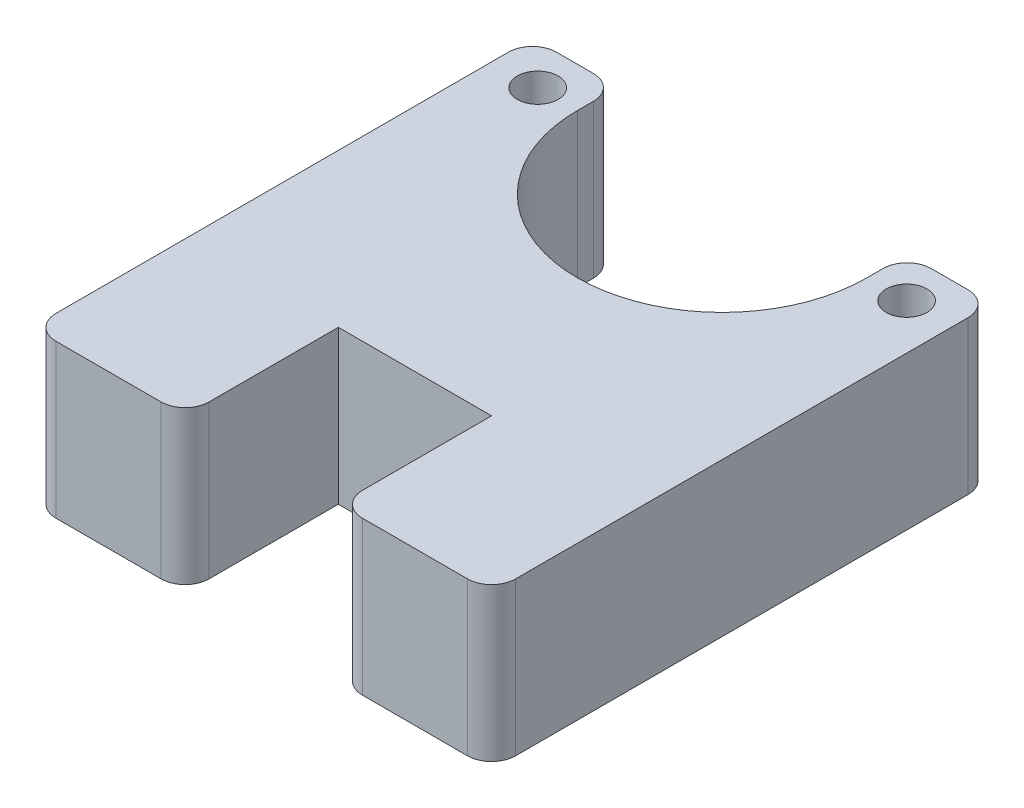
SolidWorks part; units mm, degrees
ref_plane "Front Plane" through (0, 0, 0) normal (0, 0, 1) x (1, 0, 0)
ref_plane "Top Plane" through (0, 0, 0) normal (0, 1, 0) x (1, 0, 0)
ref_plane "Right Plane" through (0, 0, 0) normal (1, 0, 0) x (0, 0, -1)
sketch "Sketch1" plane through (0, 0, 0) normal (0, 1, 0) x (1, 0, 0)
  line L0 (0, 0) -> (0, 6.0001)
  line L1 (0, 0) -> (19.05, 0)
  line L2 (0, 6.0001) -> (19.05, 6.0001)
  line L3 (19.05, 0) -> (19.05, 6.0001)
  line L4 (0, 6.0001) -> (0, 14.3937)
  line L5 (0, 6.0001) -> (3.525, 6.0001)
  line L6 (0, 14.3937) -> (3.525, 14.3937)
  line L7 (3.525, 6.0001) -> (3.525, 14.3937)
  line L8 (19.05, 6.0001) -> (19.05, 14.3937)
  line L9 (19.05, 6.0001) -> (15.525, 6.0001)
  line L10 (19.05, 14.3937) -> (15.525, 14.3937)
  line L11 (15.525, 6.0001) -> (15.525, 14.3937)
  line L12 (0, 0) -> (6.35, 0)
  line L13 (0, 0) -> (0, -6.35)
  line L14 (6.35, 0) -> (6.35, -6.35)
  line L15 (0, -6.35) -> (6.35, -6.35)
  line L16 (19.05, 0) -> (12.7, 0)
  line L17 (19.05, 0) -> (19.05, -6.35)
  line L18 (12.7, 0) -> (12.7, -6.35)
  line L19 (19.05, -6.35) -> (12.7, -6.35)
  arc A0 (3.525, 12.7287) -> (15.525, 12.7287) centre (9.525, 12.7287) ccw
  circle A1 centre (17.1675, 12.7287) radius 0.845
  circle A2 centre (1.8825, 12.7287) radius 0.845
  point P8 (9.525, 6.0001)
  dimension "D6" = 1.69
  dimension "D1" = 6.0001
  dimension "D2" = 6.35
  dimension "D3" = 6.7286
  dimension "D4" = 6
  dimension "D5" = 1.665
  dimension "D7" = 1.6425
  dimension "D9" = 6.35
  dimension "D10" = 6.35
  dimension "D11" = 6.35
  dimension "D12" = 6.35
  dimension "D13" = 1.6425
extrude "Boss-Extrude1" add sketch "Sketch1" along normal blind 6.35 contours L2 L7 L6 L4 A2 | A0 L7 L2 L11 | L11 L2 L8 L10 A1 | L1 L3 L2 L0 | L13 L15 L14 L1 | L19 L17 L1 L18
fillet "Fillet3" radius 1 8 edges at (19.05, 3.175, 6.35) (12.7, 3.175, 6.35) (6.35, 3.175, 6.35) (0, 3.175, 6.35) (19.05, 3.175, -14.3937) (15.525, 3.175, -14.3937) (3.525, 3.175, -14.3937) (0, 3.175, -14.3937)
equation "\"vigorwidth\"= 0.472441in"
equation "\"vigorflangewidth\"= 0.731102in"
equation "\"vigorflangelength\"= 0.131102in"
equation "\"vigorscrewsize\"= 0.066535in"
equation "\"vigorholeoffsetwid\"= 0.0646653in"
equation "\"vigorholeoffsetlen\"= 0.065551in"
equation "\"vigorflangedepth\"= 0.0901575in"
equation "\"vigordiscdepth\"= 0.0492126in"
equation "\"vigormotordepth\"= 1.12362in"
equation "\"vigortipdepth\"= 0.259055in"
equation "\"vigoraxlewidth\"= 0.173622in"
equation "\"vigorcutlen\"= 0.0480315in"
equation "\"vigoraxledepth\"= 0.159055in"
equation "\"D4@Sketch1\"=\"vigorwidth\"/2"
equation "\"TriggerRackOffset\"=.236224in"
equation "\"D1@Sketch1\" = \"TriggerRackOffset\""
equation "\"TriggerSlotSizeInt\"=.25in"
equation "\"D10@Sketch1\" = \"TriggerSlotSizeInt\""
equation "\"D9@Sketch1\" = \"TriggerSlotSizeInt\""
equation "\"MotorMountLegLength\"=.25in"
equation "\"D11@Sketch1\"=\"MotorMountLegLength\""
equation "\"D12@Sketch1\"=\"MotorMountLegLength\""
equation "\"GearOffset\"=.264907in"
equation "\"D3@Sketch1\"=\"GearOffset\""
equation "\"D7@Sketch1\"=\"vigorholeoffsetwid\""
equation "\"D13@Sketch1\"=\"vigorholeoffsetwid\""
equation "\"D5@Sketch1\"=\"vigorflangelength\"/2"
equation "\"TriggerSlotSpacing\"=.25in"
equation "\"D2@Sketch1\" = \"TriggerSlotSpacing\""
equation "\"D6@Sketch1\"=\"vigorscrewsize\""
equation "\"CageLeftBottomEdge\"=22.11mm"
equation "\"CageLeftTopEdge\"=22.11mm"
equation "\"CageRightBottomEdge\"=21.63mm"
equation "\"CageRightTopEdge\"=21.63mm"
equation "\"CageHeight\"=86.04mm"
equation "\"CageLength\"=73.76mm"
equation "\"CageTopScrewClearance\"=10mm"
equation "\"CageBottomScrewClearance\"=25mm"
equation "\"CageLeftTopDepth\"= 11.65mm"
equation "\"CageLeftBottomDepth\"=11.11mm"
equation "\"CageLeftTopHeight\"=8.56175mm"
equation "\"CageLeftBottomHeight\"=16mm"
equation "\"CageRightTopDepth\"= 11.05mm"
equation "\"CageRightBottomDepth\"=10.58mm"
equation "\"CageRightTopHeight\"=9.6mm"
equation "\"CageRightBottomHeight\"=15.49mm"
equation "\"CageLeftTopChannelDepth\"=2.41908mm"
equation "\"CageLeftBottomChannelDepth\"=2.588mm"
equation "\"CageLeftChannelHeight\"=11.7mm"
equation "\"CageRightTopChannelDepth\"=2.32mm"
equation "\"CageRightBottomChannelDepth\"=2.318mm"
equation "\"CageRightChannelHeight\"=10mm"
equation "\"CageChanRelHeight\"=23.99mm"
equation "\"CageChanRelDepth\"=5.492mm"
equation "\"CageChamberRadius\"=16.261mm"
equation "\"CageScrewDiameter\"=4.8mm"
equation "\"CageSetScrewDiameter\"=3.5mm"
equation "\"CageAxleRadius\"=6.639mm"
equation "\"CageAxleKeyHeight\"=1.619mm"
equation "\"CageAxleKeyWidth\"=2.662mm"
equation "\"CageHoseWindowWidth\"=16.29mm"
equation "\"CageHoseWindowHeight\"=26.5mm"
equation "\"CageHoseWindow-Edge\"=8.89mm"
equation "\"CageScrew-VerticalEdge\"=5.0mm"
equation "\"CageScrew-HorizontalEdge\"=7.5mm"
equation "\"CageScrew-HoseCornerScrewEdge\"=4.45mm"
equation "\"CageAxle-BottomEdge\"=56.05mm"
equation "\"CageAxle-FrontEdge\"=46.03mm"
equation "\"CageBackSetScrew-Axle\"=40mm"
equation "\"CageFrontSetScrew-Axle\"=22mm"
equation "\"CageVelocityWindow-BackEdge\"=34.8mm"
equation "\"CageVelocityWindow-BottomEdge\"=27.55mm"
equation "\"CageVelocityWindowHeight\"=22.29mm"
equation "\"CageVelocityWindowWidth\"=12.61mm"
equation "\"TriggerSlot-BottomEdge\"=6.35mm"
equation "\"TriggerSlot-FrontEdge\"=15mm"
equation "\"TriggerSlotSize\"=6.7mm"
equation "\"TriggerMiniSlotWidth\"=3.5mm"
equation "\"TriggerRackWidth\"=6.5mm"
equation "\"TGMGearFaceDiameter\"=24.40mm"
equation "\"TGMCylinderLength\"=15.00mm"
equation "\"TGMScrewHole-Center\"=8.70mm"
equation "\"TGMScrewHoleDiameter\"=5.04mm"
equation "\"TGMCenterHoleDiameter\"=9.50mm"
equation "\"TGMShaftCollarSideLength\"=19.00mm"
equation "\"TGMShaftCollarDockingDepth\"=7.00mm"
equation "\"whitemotordepth\"=11.27mm"
equation "\"whitemotorbackdepth\"=3.845mm"
equation "\"whitemotoraxledepth\" = 3.5mm"
equation "\"whitemotoraxleoffset\"=11.4mm"
equation "\"whitemotorwidth\"=12.07mm"
equation "\"whitemotorheight\"=16.68mm"
equation "\"whitemotorcylinderlength\" =13.04mm"
equation "\"whitemotorcylinderradius\"=3.845mm"
equation "\"whitemotorcylinderoffset\"=2.35mm"
equation "\"whitemotorcutoutlength\"=1.88mm"
equation "\"whitemotorouterrad\"=5mm"
